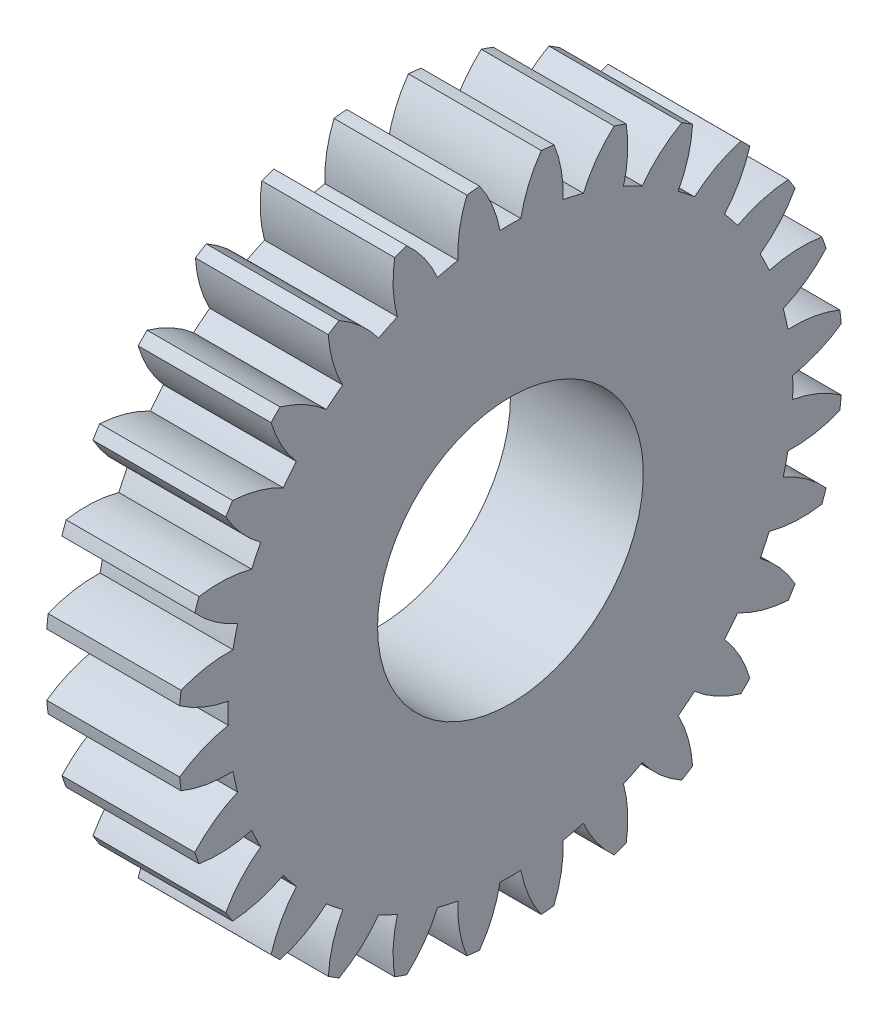
SolidWorks part; units mm, degrees
ref_plane "Plane1" through (0, 0, 0) normal (0, 0, 1) x (1, 0, 0)
ref_plane "Plane2" through (0, 0, 0) normal (0, 1, 0) x (1, 0, 0)
ref_plane "Plane3" through (0, 0, 0) normal (1, 0, 0) x (0, 0, -1)
sketch "HoldingSke" plane through (0, 0, 0) normal (0, 1, 0) x (1, 0, 0)
  line L0 (0, 0) -> (1.7659, -0.9389)
  line L1 (-15, 0) -> (100, 0) construction
  line L2 (0, 0) -> (-2.1039, 2.3779)
  line L3 (0, 0) -> (-11.863, 4.5341)
  line L4 (0, 0) -> (7.6251, 4.0544)
  line L5 (0, 0) -> (-46.8476, -17.4728)
  line L6 (0, 0) -> (-2.4869, -1.6779)
  line L7 (-2.1039, 2.3779) -> (8.6586, 51.2059)
  line L8 (-76.2, 54.61) -> (-75.2, 54.61)
  line L9 (-71.009, 38.7566) -> (-53.1078, 45.2721)
  line L10 (-76.2, 71.12) -> (104.1128, 71.12)
  line L11 (0, 0) -> (-3, 0)
  line L12 (-76.2, 101.6) -> (-76.181, 101.6)
  line L13 (24.9733, 27.94) -> (52.9518, 28.4284)
  line L14 (24.9733, 27.94) -> (24.9743, 27.94)
  line L15 (24.9733, 27.94) -> (100.4006, 29.5858)
  line L16 (-63.627, -0.5) -> (-12.827, -0.5)
  circle A0 centre (0, 0) radius 3
  circle A1 centre (0, 0) radius 6.374
  circle A2 centre (0, 0) radius 37.5
  circle A3 centre (0, 0) radius 3
  dimension "MHD" = 12.748
  dimension "Hub_dia" = 75
  dimension "Bore" = 6
  dimension "MBD" = 6
  dimension "Num_teeth" = 28
  dimension "Pitch_radius" = 180.3128
  dimension "Pitch" = 2
  dimension "Width" = 3
  dimension "Overall_len" = 50
  dimension "Show_teeth" = 28
  dimension "Thickness" = 3
  dimension "OAL" = 50.0001
  dimension "T_dim" = 1
  dimension "Ap" = 20
  dimension "H" = 19.05
  dimension "Backlash" = 0.019
  dimension "Addendum_fac" = 1
  dimension "Dedendum_fac" = 1.25
  dimension "Clearance_fac" = 0.25
  dimension "Dedendum_add" = 0.001
  dimension "Module" = 0.5
sketch "BasProSke" plane through (0, 0, 0) normal (0, 1, 0) x (1, 0, 0)
  line L0 (-10, 0) -> (60, 0) construction
  line L1 (0, 0) -> (0, 7.5)
  line L2 (0, 0) -> (3, 0)
  line L3 (3, 0) -> (3, 7.5)
  line L4 (3, 7.5) -> (0, 7.5)
  dimension "Diameter" = 15
  dimension "Thickness" = 3
revolve "Base-Revolve" add sketch "BasProSke" angle 360 about L0
sketch "TooCutSke" plane through (0, 0, 0) normal (1, 0, 0) x (0, 0, -1)
  line L1 (0, 0) -> (0, 107) construction
  line L2 (0, 0) -> (-0.4257, 6.987) construction
  line L3 (0, 0) -> (-1.5654, 13.8936) construction
  line L4 (-0.4257, 6.987) -> (-0.7827, 6.9468) construction
  arc A0 (0.2356, 6.3696) -> (-0.2356, 6.3696) centre (0, 0) ccw
  arc A1 (0.7134, 7.4915) -> (-0.7134, 7.4915) centre (0, 0) ccw
  circle A2 centre (0, 0) radius 7 construction
  circle A3 centre (0, 0) radius 6.5778 construction
  arc A4 (-0.2356, 6.3696) -> (-0.7134, 7.4915) centre (-2.9887, 5.8597) ccw
  arc A5 (0.7134, 7.4915) -> (0.2356, 6.3696) centre (2.9887, 5.8597) ccw
  dimension "Root_dia" = 12.748
  dimension "Overcut_dia" = 15.0508
  dimension "Pitch_dia" = 14
  dimension "Base_dia" = 13.1557
  dimension "Flank_rad" = 2.8
  dimension "Half_ang" = 6.429
  dimension "Half_CT" = 0.3592
extrude "ToothCut" cut sketch "TooCutSke" along normal through all
fillet "Breaks" [suppressed] radius 0.01
fillet "RootFillets" [suppressed] radius 0.126
pattern_circular "TeethCuts" count 28 every 12.857 about axis through (-10, 0, 0) along (1, 0, 0) of "ToothCut", "RootFillets", "Breaks"
sketch "HubNeaOneSke" plane through (0, 0, 0) normal (-1, 0, 0) x (0, 0, 1)
  circle A0 centre (0, 0) radius 6.374
  dimension "Diameter" = 12.748
extrude "HubNearOne" [suppressed] add sketch "HubNeaOneSke" along normal blind 47.0001
sketch "HubNeaBotSke" plane through (0, 0, 0) normal (-1, 0, 0) x (0, 0, 1)
  circle A0 centre (0, 0) radius 6.374
  dimension "Diameter" = 12.748
extrude "HubNearBoth" [suppressed] add sketch "HubNeaBotSke" along normal blind 23.5
ref_plane "FarPln" through (3, 0, 0) normal (1, 0, 0) x (0, 0, -1)
sketch "HubFarSke" plane through (3, 0, 0) normal (1, 0, 0) x (0, 0, -1)
  circle A0 centre (0, 0) radius 6.374
  dimension "Diameter" = 12.748
extrude "HubFar" [suppressed] add sketch "HubFarSke" along normal blind 23.5
sketch "BorSke" plane through (0, 0, 0) normal (1, 0, 0) x (0, 0, -1)
  circle A0 centre (0, 0) radius 3
  dimension "Diameter" = 6
extrude "Bore" cut sketch "BorSke" along normal mid plane 100.0001
sketch "KeySke" plane through (0, 0, 0) normal (1, 0, 0) x (0, 0, -1)
  line L0 (-1, 0) -> (-1, 4)
  line L1 (-1, 4) -> (1, 4)
  line L2 (1, 4) -> (1, 0)
  line L3 (0, 0) -> (0, 34) construction
  line L4 (-1, 0) -> (1, 0)
  dimension "Offset" = 4
  dimension "Width" = 2
extrude "Keyway" [suppressed] cut sketch "KeySke" along normal mid plane 100.0001
pattern_circular "Keyway2" [suppressed] count 2 every 90 about axis through (-10, 0, 0) along (1, 0, 0)
equation "' \"Module@HoldingSke\" = 6.35"
equation "' \"Num_teeth@HoldingSke\" = 12"
equation "' \"Ap@HoldingSke\" =  20"
equation "' \"Width@HoldingSke\" = 0.5 * 25.4"
equation "' \"Hub_dia@HoldingSke\"= 1 * 25.4"
equation "' \"Overall_len@HoldingSke\" = 1.0 * 25.4"
equation "' \"Bore@HoldingSke\" = 0.75 * 25.4"
equation "' \"T_dim@HoldingSke\" = 0.1 * 25.4"
equation "' \"Width@KeySke\" = 0.25 * 25.4"
equation "' \"Show_teeth@HoldingSke\" = 13"
equation "' \"Backlash@HoldingSke\" = 0.009 * 25.4"
equation "' \"Addendum_fac@HoldingSke\" = 1.0"
equation "' \"Dedendum_fac@HoldingSke\" = 1.25"
equation "' \"Dedendum_add@HoldingSke\" = 0.00005 * 25.4"
equation "' \"Clearance_fac@HoldingSke\" = 0.25"
equation "\"Pitch@HoldingSke\" = 1 / \"Module@HoldingSke\""
equation "\"Overcut_dia@TooCutSke\" = (\"Num_teeth@HoldingSke\" + 2 * \"Addendum_fac@HoldingSke\") / \"Pitch@HoldingSke\" + 0.002 * 25.4"
equation "\"Pitch_dia@TooCutSke\" = \"Num_teeth@HoldingSke\" / \"Pitch@HoldingSke\""
equation "\"Base_dia@TooCutSke\" = \"Num_teeth@HoldingSke\" / \"Pitch@HoldingSke\" * cos((\"Ap@HoldingSke\"  * 3.14159265 / 180))"
equation "\"Root_dia@TooCutSke\" = (\"Num_teeth@HoldingSke\" + 2) / \"Pitch@HoldingSke\" - 2 * (\"Addendum_fac@HoldingSke\" + \"Dedendum_fac@HoldingSke\") / \"Pitch@HoldingSke\" - \"Dedendum_add@HoldingSke\" * 2"
equation "\"Half_ang@TooCutSke\" = 180 / \"Num_teeth@HoldingSke\""
equation "\"Half_CT@TooCutSke\" = \"Num_teeth@HoldingSke\" / \"Pitch@HoldingSke\" * sin((3.14159265 / 2 / \"Num_teeth@HoldingSke\")) / 2 - 7 * \"Backlash@HoldingSke\" / 4"
equation "\"Flank_rad@TooCutSke\" = \"Num_teeth@HoldingSke\" / \"Pitch@HoldingSke\" / 5"
equation "\"Radius@RootFillets\" = \"Clearance_fac@HoldingSke\" / \"Pitch@HoldingSke\" + \"Dedendum_add@HoldingSke\""
equation "\"Break_rad@Breaks\" = 0.02 / \"Pitch@HoldingSke\""
equation "\"Thickness@HoldingSke\" = \"Width@HoldingSke\""
equation "\"OAL@HoldingSke\" = \"Thickness@HoldingSke\""
equation "\"MHD@HoldingSke\" = (\"Num_teeth@HoldingSke\" + 2) / \"Pitch@HoldingSke\" - 2 * (\"Addendum_fac@HoldingSke\" + \"Dedendum_fac@HoldingSke\")  / \"Pitch@HoldingSke\" - \"Dedendum_add@HoldingSke\" * 2"
equation "\"MBD@HoldingSke\" = (\"Num_teeth@HoldingSke\" + 2) / \"Pitch@HoldingSke\" - 2 * (\"Addendum_fac@HoldingSke\" + \"Dedendum_fac@HoldingSke\")  / \"Pitch@HoldingSke\" - \"Dedendum_add@HoldingSke\" * 2 - 0.002 * 25.4"
equation "\"MHD@HoldingSke\" = ((sgn( \"MHD@HoldingSke\" - \"Hub_dia@HoldingSke\" )-1)*( \"MHD@HoldingSke\" - \"Hub_dia@HoldingSke\" ))/-2+ \"Hub_dia@HoldingSke\""
equation "\"MBD@HoldingSke\" = ((sgn( \"MBD@HoldingSke\" - \"Bore@HoldingSke\" )-1)*( \"MBD@HoldingSke\" - \"Bore@HoldingSke\" ))/-2+ \"Bore@HoldingSke\""
equation "\"OAL@HoldingSke\" = ((sgn( \"OAL@HoldingSke\" - \"Overall_len@HoldingSke\" )+1)*( \"OAL@HoldingSke\" - \"Overall_len@HoldingSke\" ))/2 + \"Overall_len@HoldingSke\" + 0.000002 * 25.4"
equation "\"Num_teeth@TeethCuts\" = int( \"Show_teeth@HoldingSke\" ) + 1"
equation "\"Num_teeth@TeethCuts\" = ((sgn( \"Num_teeth@TeethCuts\" - \"Num_teeth@HoldingSke\" )-1)*( \"Num_teeth@TeethCuts\" - \"Num_teeth@HoldingSke\" ))/-2+ \"Num_teeth@HoldingSke\""
equation "\"Num_teeth@TeethCuts\" = ((sgn( \"Num_teeth@TeethCuts\" - 2.0)+1)*( \"Num_teeth@TeethCuts\" - 2.0))/2 +2.0"
equation "\"Angle@TeethCuts\" = 360.0 / \"Num_teeth@HoldingSke\""
equation "\"Diameter@BasProSke\" = (\"Num_teeth@HoldingSke\" + 2 * \"Addendum_fac@HoldingSke\") / \"Pitch@HoldingSke\""
equation "\"Thickness@BasProSke\"  = \"Thickness@HoldingSke\""
equation "' \"Fillet_rad@BasProSke\" =  \"Thickness@HoldingSke\" * 0.05"
equation "\"MHD@HoldingSke\" = ((sgn( \"MHD@HoldingSke\" - \"Root_dia@TooCutSke\" )-1)*( \"MHD@HoldingSke\" - \"Root_dia@TooCutSke\" ))/-2+ \"Root_dia@TooCutSke\""
equation "\"Diameter@HubNeaOneSke\" = \"MHD@HoldingSke\""
equation "\"Length@HubNearOne\" = \"OAL@HoldingSke\" - \"Thickness@BasProSke\""
equation "\"Diameter@HubNeaBotSke\" = \"MHD@HoldingSke\""
equation "\"Length@HubNearBoth\" = ( \"OAL@HoldingSke\" - \"Thickness@BasProSke\" ) / 2.0"
equation "\"Thickness@FarPln\" = \"Thickness@BasProSke\""
equation "\"Diameter@HubFarSke\" = \"MHD@HoldingSke\""
equation "\"Length@HubFar\" = ( \"OAL@HoldingSke\" - \"Thickness@BasProSke\" ) / 2.0"
equation "\"Diameter@BorSke\" = \"MBD@HoldingSke\""
equation "\"D1@Bore\" = \"OAL@HoldingSke\" * 2.0"
equation "\"D1@Keyway\" = \"OAL@HoldingSke\" * 2.0"
equation "\"Offset@KeySke\" = \"T_dim@HoldingSke\" + \"MBD@HoldingSke\" / 2.0"
